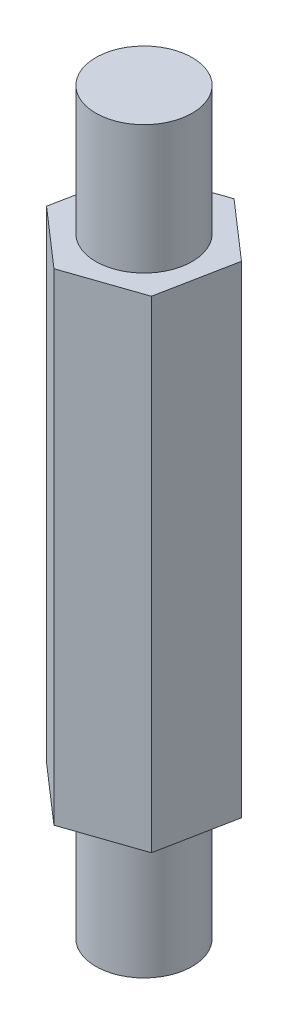
SolidWorks part; units mm, degrees
ref_plane "Front Plane" through (0, 0, 0) normal (0, 0, 1) x (1, 0, 0)
ref_plane "Top Plane" through (0, 0, 0) normal (0, 1, 0) x (1, 0, 0)
ref_plane "Right Plane" through (0, 0, 0) normal (1, 0, 0) x (0, 0, -1)
sketch "Sketch1" plane through (0, 0, 0) normal (0, 1, 0) x (1, 0, 0)
  line L1 (1.8002, -1.5692) -> (2.2591, 0.7744)
  line L2 (2.2591, 0.7744) -> (0.4589, 2.3436)
  line L3 (0.4589, 2.3436) -> (-1.8002, 1.5692)
  line L4 (-1.8002, 1.5692) -> (-2.2591, -0.7744)
  line L5 (-2.2591, -0.7744) -> (-0.4589, -2.3436)
  line L6 (-0.4589, -2.3436) -> (1.8002, -1.5692)
  circle A0 centre (0, 0) radius 2.0682 construction
extrude "Boss-Extrude1" add sketch "Sketch1" along normal blind 15
sketch "Sketch2" plane through (0, 15, 0) normal (0, 1, 0) x (1, 0, 0)
  circle A0 centre (0, 0) radius 1.5
  dimension "D1" = 3
extrude "Boss-Extrude2" add sketch "Sketch2" along normal blind 4
sketch "Sketch3" plane through (0, 0, 0) normal (0, -1, 0) x (1, 0, 0)
  circle A0 centre (0, 0) radius 1.5
  dimension "D1" = 3
extrude "Boss-Extrude3" add sketch "Sketch3" along normal blind 4
